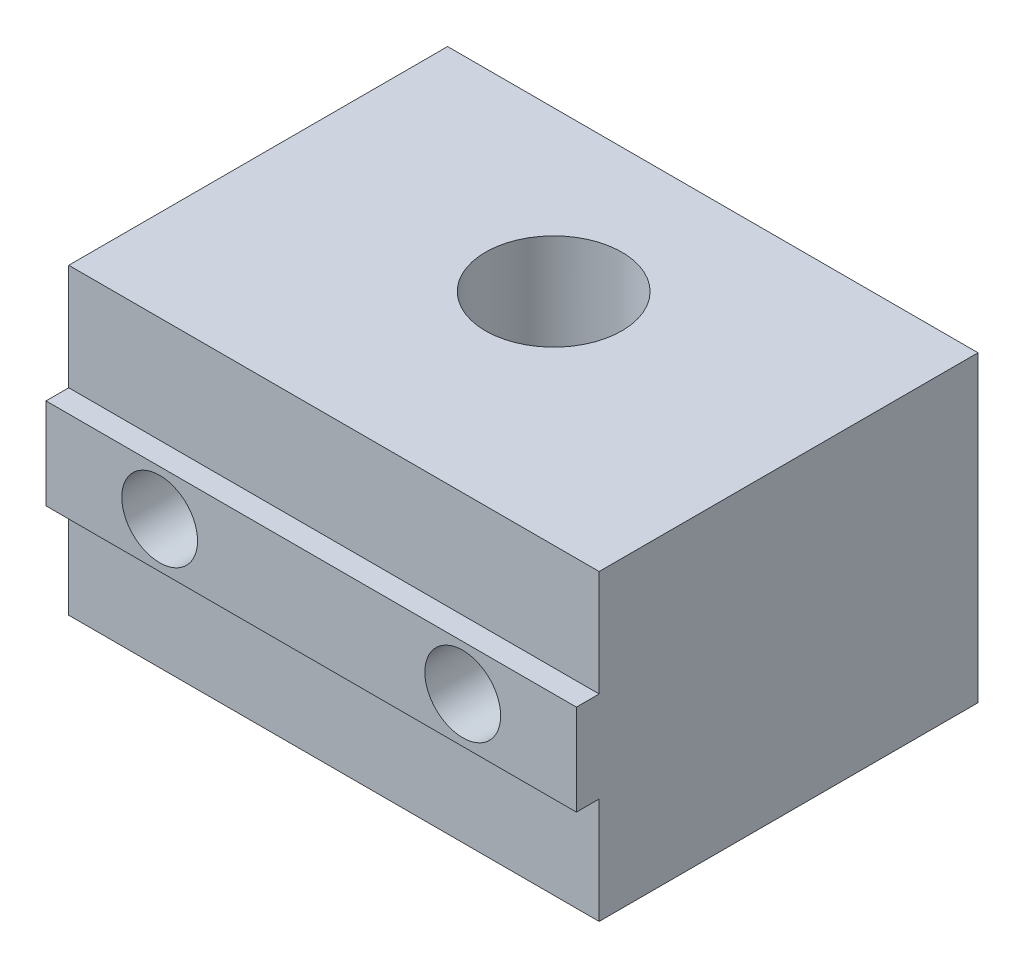
SolidWorks part; units mm, degrees
ref_plane "Front" through (0, 0, 0) normal (0, 0, 1) x (1, 0, 0)
ref_plane "Top" through (0, 0, 0) normal (0, 1, 0) x (1, 0, 0)
ref_plane "Right" through (0, 0, 0) normal (1, 0, 0) x (0, 0, -1)
sketch "Sketch1" plane through (0, 0, 0) normal (0, 1, 0) x (1, 0, 0)
  line L1 (0, 0) -> (35, 0)
  line L2 (0, 0) -> (0, 25)
  line L3 (0, 25) -> (35, 25)
  line L4 (35, 0) -> (35, 25)
  dimension "D1" = 35
  dimension "D2" = 25
extrude "Boss-Extrude1" add sketch "Sketch1" along normal blind 20
sketch "Sketch5" plane through (35, 0, 0) normal (1, 0, 0) x (0, 0, -1)
  line L0 (0, 20) -> (0, 0) construction
  line L1 (0, 13) -> (-1.5, 13)
  line L2 (0, 13) -> (0, 7)
  line L3 (0, 7) -> (-1.5, 7)
  line L4 (-1.5, 13) -> (-1.5, 7)
  point P6 (0, 10)
  point P7 (0, 10)
  dimension "D1" = 6
  dimension "D2" = 1.5
extrude "Boss-Extrude2" add sketch "Sketch5" against normal through all
sketch "Sketch2" plane through (0, 20, 0) normal (0, 1, 0) x (1, 0, 0)
  line L0 (0, 0) -> (35, 0) construction
  line L1 (35, 25) -> (0, 25) construction
  circle A0 centre (17.5, 14.5) radius 4.5
  point P6 (17.5, 25)
  dimension "D2" = 9
  dimension "D1" = 14.5
extrude "Cut-Extrude1" cut sketch "Sketch2" against normal through all
sketch "Sketch3" plane through (0, 0, -25) normal (0, 0, -1) x (-1, 0, 0)
  line L0 (-7.5, 10) -> (-27.5, 10) construction
  line L1 (-35, 0) -> (0, 0) construction
  line L2 (-35, 20) -> (-35, 0) construction
  circle A0 centre (-7.5, 10) radius 2.5
  circle A1 centre (-27.5, 10) radius 2.5
  point P4 (-17.5, 10)
  point P7 (-17.5, 0)
  point P10 (-35, 10)
  dimension "D1" = 5
  dimension "D2" = 5
  dimension "D3" = 20
extrude "Cut-Extrude4" cut sketch "Sketch3" against normal through all
sketch "Sketch4" plane through (0, 0, -25) normal (0, 0, -1) x (-1, 0, 0)
  circle A0 centre (-7.5, 10) radius 5
  circle A1 centre (-27.5, 10) radius 5
  circle M1 centre (-27.5, 10) radius 2.5
  circle M2 centre (-7.5, 10) radius 2.5
  dimension "D1" = 10
  dimension "D2" = 10
extrude "Cut-Extrude5" cut sketch "Sketch4" against normal blind 5 contours A0 M2 | A1 M1
equation "\"D2@Sketch3\"=\"D1@Sketch3\""
equation "\"D3@Sketch3\"=\"D2@Sketch2\" + \"D1@Sketch3\" + 6"
equation "\"D2@Sketch4\"=\"D1@Sketch4\""
